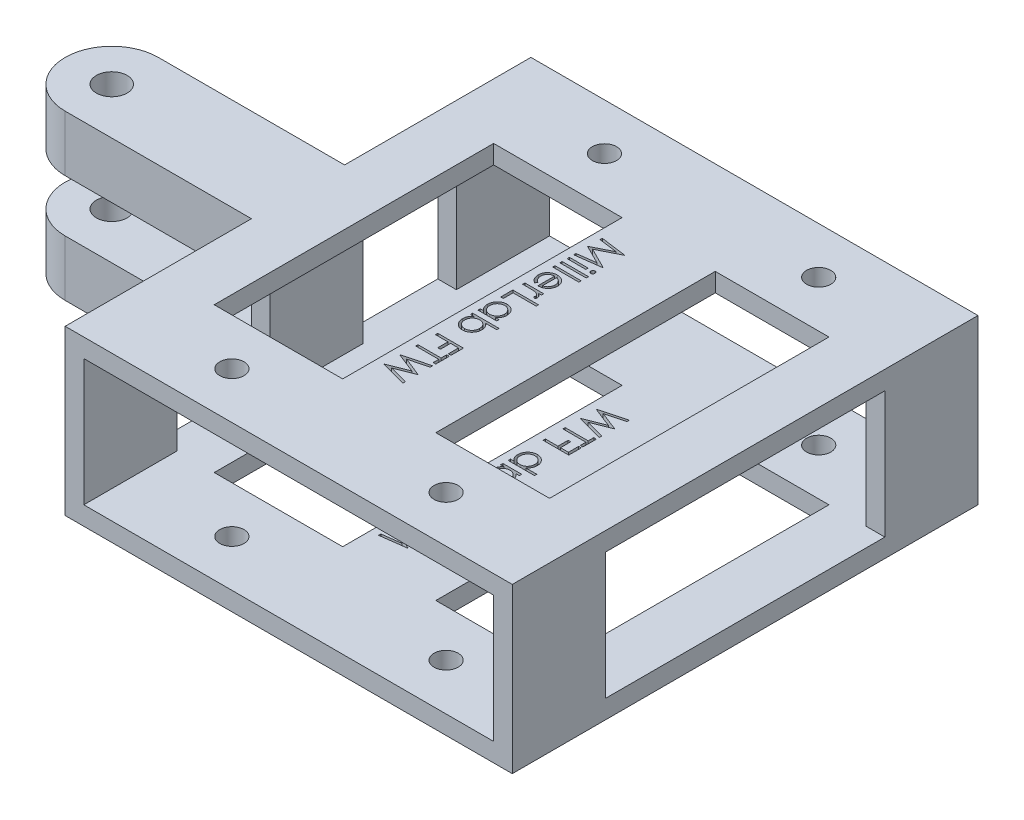
SolidWorks part; units mm, degrees
ref_plane "Front Plane" through (0, 0, 0) normal (0, 0, 1) x (1, 0, 0)
ref_plane "Top Plane" through (0, 0, 0) normal (0, 1, 0) x (1, 0, 0)
ref_plane "Right Plane" through (0, 0, 0) normal (1, 0, 0) x (0, 0, -1)
sketch "Sketch1" plane through (0, 0, 0) normal (0, 0, 1) x (1, 0, 0)
  line L0 (-30.48, -11.176) -> (30.48, -11.176)
  line L1 (-27.94, -8.636) -> (27.94, -8.636)
  line L2 (-27.94, -8.636) -> (-27.94, 8.636)
  line L3 (-27.94, 8.636) -> (27.94, 8.636)
  line L4 (27.94, -8.636) -> (27.94, 8.636)
  line L5 (-27.94, -8.636) -> (27.94, 8.636) construction
  line L6 (-27.94, 8.636) -> (27.94, -8.636) construction
  line L7 (30.48, -11.176) -> (30.48, 11.176)
  line L8 (-30.48, 11.176) -> (30.48, 11.176)
  line L9 (-30.48, -11.176) -> (-30.48, 11.176)
  point P0 (0, 0)
  dimension "D1" = 55.88
  dimension "D2" = 17.272
  dimension "D3" = 2.54
extrude "Boss-Extrude1" add sketch "Sketch1" against normal blind 12.7
sketch "Sketch2" plane through (0, 0, -12.7) normal (0, 0, -1) x (-1, 0, 0)
  line L0 (-27.94, 8.636) -> (27.94, 8.636) construction
  line L1 (-30.48, 11.176) -> (-22.86, 11.176)
  line L2 (-30.48, 11.176) -> (-30.48, 8.636)
  line L3 (-30.48, 8.636) -> (-22.86, 8.636)
  line L4 (-22.86, 11.176) -> (-22.86, 8.636)
  line L5 (-7.3566, 8.636) -> (-7.3566, 11.176)
  line L6 (-7.3566, 8.636) -> (5.3434, 8.636)
  line L7 (-7.3566, 11.176) -> (5.3434, 11.176)
  line L8 (5.3434, 8.636) -> (5.3434, 11.176)
  line L9 (-7.3566, 8.636) -> (5.3434, 11.176) construction
  line L10 (-7.3566, 11.176) -> (5.3434, 8.636) construction
  line L11 (-30.48, 0) -> (46.0926, 0) construction
  line L12 (30.48, 11.176) -> (22.86, 11.176)
  line L13 (30.48, 11.176) -> (30.48, 8.636)
  line L14 (30.48, 8.636) -> (22.86, 8.636)
  line L15 (22.86, 11.176) -> (22.86, 8.636)
  line L17 (-7.3566, -11.176) -> (5.3434, -8.636) construction
  line L18 (-7.3566, -8.636) -> (5.3434, -11.176) construction
  line L19 (22.86, -11.176) -> (22.86, -8.636)
  line L20 (30.48, -8.636) -> (22.86, -8.636)
  line L21 (30.48, -11.176) -> (30.48, -8.636)
  line L22 (30.48, -11.176) -> (22.86, -11.176)
  line L23 (5.3434, -8.636) -> (5.3434, -11.176)
  line L24 (-7.3566, -11.176) -> (5.3434, -11.176)
  line L25 (-7.3566, -8.636) -> (5.3434, -8.636)
  line L26 (-7.3566, -8.636) -> (-7.3566, -11.176)
  line L27 (-22.86, -11.176) -> (-22.86, -8.636)
  line L28 (-30.48, -8.636) -> (-22.86, -8.636)
  line L29 (-30.48, -11.176) -> (-30.48, -8.636)
  line L30 (-30.48, -11.176) -> (-22.86, -11.176)
  point P8 (-1.0066, 9.906)
  point P32 (-1.0066, -9.906)
  dimension "D1" = 7.62
  dimension "D2" = 12.7
extrude "Boss-Extrude2" add sketch "Sketch2" along normal blind 38.1
sketch "Sketch4" plane through (0, 0, -50.8) normal (0, 0, -1) x (-1, 0, 0)
  line L1 (-30.48, 11.176) -> (30.48, 11.176)
  line L2 (-30.48, 11.176) -> (-30.48, -11.176)
  line L3 (-30.48, -11.176) -> (30.48, -11.176)
  line L4 (30.48, 11.176) -> (30.48, -11.176)
  line L5 (-27.94, 8.636) -> (27.94, 8.636)
  line L6 (-27.94, 8.636) -> (-27.94, -8.636)
  line L7 (-27.94, -8.636) -> (27.94, -8.636)
  line L8 (27.94, 8.636) -> (27.94, -8.636)
extrude "Boss-Extrude3" add sketch "Sketch4" along normal blind 12.7
sketch "Sketch5" plane through (0, 11.176, 0) normal (0, 1, 0) x (1, 0, 0)
  line L0 (22.86, 12.7) -> (30.48, 12.7) construction
  line L1 (30.48, 63.5) -> (30.48, 0) construction
  line L2 (30.48, 12.7) -> (30.48, 0) construction
  line L3 (-30.48, 31.75) -> (30.48, 31.75) construction
  line L5 (-30.48, 63.5) -> (-30.48, 0) construction
  circle A0 centre (-14.1017, 6.35) radius 1.9939
  circle A1 centre (15.1083, 6.35) radius 1.9939
  circle A2 centre (15.1083, 57.15) radius 1.9939
  circle A3 centre (-14.1017, 57.15) radius 1.9939
  point P21 (-14.1017, 6.35)
  point P22 (15.1083, 6.35)
  dimension "D1" = 3.9878
  dimension "D2" = 3.9878
sketch "Sketch6" plane through (-30.48, 0, 0) normal (-1, 0, 0) x (0, 0, 1)
  line L0 (-63.5, 11.176) -> (0, 11.176) construction
  line L1 (-38.1, 11.176) -> (-25.4, 11.176)
  line L2 (-38.1, 11.176) -> (-38.1, -11.176)
  line L3 (-38.1, -11.176) -> (-25.4, -11.176)
  line L4 (-25.4, 11.176) -> (-25.4, -11.176)
  line L5 (-63.5, -11.176) -> (0, -11.176) construction
  line L7 (-50.8, -8.636) -> (-50.8, 8.636) construction
  dimension "D1" = 12.7
  dimension "D2" = 12.7
extrude "Boss-Extrude4" add sketch "Sketch6" against normal blind 2.54
sketch "Sketch7" plane through (-30.48, 0, 0) normal (-1, 0, 0) x (0, 0, 1)
  line L0 (-25.4, -8.636) -> (-25.4, 8.636) construction
  line L3 (-38.1, 8.636) -> (-25.4, 8.636)
  line L4 (-38.1, 8.636) -> (-38.1, 3.556)
  line L5 (-38.1, 3.556) -> (-25.4, 3.556)
  line L6 (-25.4, 8.636) -> (-25.4, 3.556)
  line L8 (-38.1, -8.636) -> (-25.4, -8.636)
  line L9 (-38.1, -8.636) -> (-38.1, -3.556)
  line L10 (-38.1, -3.556) -> (-25.4, -3.556)
  line L11 (-25.4, -8.636) -> (-25.4, -3.556)
  dimension "D1" = 5.08
extrude "Boss-Extrude5" add sketch "Sketch7" along normal blind 25.4
sketch "Sketch8" plane through (-55.88, 0, 0) normal (-1, 0, 0) x (0, 0, 1)
  line L0 (-31.75, 8.636) -> (-31.75, -8.636) construction
  line L1 (-25.4, 8.636) -> (-38.1, 8.636) construction
  line L2 (-38.1, -8.636) -> (-25.4, -8.636) construction
  line L4 (-31.75, 8.636) -> (-25.4, 8.636)
  line L5 (-31.75, 8.636) -> (-31.75, 3.556)
  line L6 (-31.75, 3.556) -> (-25.4, 3.556)
  line L7 (-25.4, 8.636) -> (-25.4, 3.556)
  line L8 (-25.4, -8.636) -> (-31.75, -8.636)
  line L9 (-25.4, -8.636) -> (-25.4, -3.556)
  line L10 (-25.4, -3.556) -> (-31.75, -3.556)
  line L11 (-31.75, -8.636) -> (-31.75, -3.556)
  dimension "D1" = 5.08
revolve "Revolve2" add sketch "Sketch8" angle 180 about L0
sketch "Sketch10" plane through (0, 8.636, 0) normal (0, 1, 0) x (1, 0, 0)
  line L0 (-55.88, 38.1) -> (-55.88, 25.4) construction
  line L1 (-62.23, 31.75) -> (-55.88, 31.75) construction
  arc A0 (-55.88, 38.1) -> (-55.88, 25.4) centre (-55.88, 31.75) ccw construction
  circle A1 centre (-55.88, 31.75) radius 2.0955
  dimension "D1" = 4.191
extrude "Cut-Extrude4" cut sketch "Sketch10" against normal through all
sketch "Sketch11" plane through (0, -11.176, 0) normal (0, -1, 0) x (-1, 0, 0)
  line L0 (4.2476, 12.7) -> (4.2476, 50.8) construction
  text T0 "MillerLab FTW"
extrude "Cut-Extrude7" cut sketch "Sketch11" against normal blind 2.54
sketch "Sketch14" plane through (0, 11.176, 0) normal (0, 1, 0) x (1, 0, 0)
  line L0 (-5.3434, 50.8) -> (-4.2476, 50.8) construction
  line L1 (-4.2476, 50.8) -> (-4.2476, 12.7) construction
  line L2 (-4.2476, 12.7) -> (-5.3434, 12.7) construction
  text T0 "MillerLab FTW"
extrude "Cut-Extrude8" cut sketch "Sketch14" against normal blind 2.54
hole_wizard "M4x0.7 Tapped Hole1" positions "Sketch16" profile "Sketch15" tap size "M4x0.7" standard "ANSI Metric" end condition through all
sketch "Sketch16" plane through (0, 11.176, 0) normal (0, 1, 0) x (1, 0, 0)
  point P0 (-14.1017, 57.15)
  point P3 (15.1083, 57.15)
  point P6 (15.1083, 6.35)
  point P9 (-14.1017, 6.35)
sketch "Sketch15" plane through (-14.1017, 11.176, -57.15) normal (1, 0, 0) x (0, 0, 1)
  line L0 (0, 0) -> (0, 22.352)
  line L1 (0, 22.352) -> (1.65, 22.352)
  line L2 (1.65, 22.352) -> (1.65, 0)
  line L5 (1.65, 0) -> (0, 0)
  line L11 (0, -6.35) -> (0, 107.95) construction
  dimension "Thru Tap Drill Dia." = 3.3
  dimension "Thru Tap Drill Depth" = 22.352
cosmetic thread "Hole Thread1" parameters "D2"=4
cosmetic thread "Hole Thread2" parameters "D2"=4
cosmetic thread "Hole Thread3" parameters "D2"=4
cosmetic thread "Hole Thread4" parameters "D2"=4
sketch "Sketch17" plane through (0, 8.636, 0) normal (0, 1, 0) x (1, 0, 0)
  line L0 (-55.88, 25.4) -> (-30.48, 25.4) construction
  line L1 (-55.88, 38.1) -> (-30.48, 38.1) construction
  line L2 (-30.48, 25.4) -> (-30.48, 38.1) construction
  line L3 (-55.88, 25.4) -> (-30.48, 25.4)
  line L4 (-55.88, 38.1) -> (-30.48, 38.1)
  line L5 (-30.48, 25.4) -> (-30.48, 38.1)
  arc A0 (-55.88, 38.1) -> (-55.88, 25.4) centre (-55.88, 31.75) ccw construction
  circle A1 centre (-55.88, 31.75) radius 2.0955 construction
  arc A2 (-55.88, 38.1) -> (-55.88, 25.4) centre (-55.88, 31.75) ccw
  circle A3 centre (-55.88, 31.75) radius 2.0955
extrude "Boss-Extrude6" add sketch "Sketch17" along normal blind 2.54
sketch "Sketch18" plane through (0, -8.636, 0) normal (0, -1, 0) x (1, 0, 0)
  line L0 (-30.48, -38.1) -> (-30.48, -25.4) construction
  line L1 (-55.88, -38.1) -> (-30.48, -38.1) construction
  line L2 (-55.88, -25.4) -> (-30.48, -25.4) construction
  line L3 (-30.48, -38.1) -> (-30.48, -25.4)
  line L4 (-55.88, -38.1) -> (-30.48, -38.1)
  line L5 (-55.88, -25.4) -> (-30.48, -25.4)
  arc A0 (-55.88, -25.4) -> (-55.88, -38.1) centre (-55.88, -31.75) ccw construction
  circle A1 centre (-55.88, -31.75) radius 2.0955 construction
  arc A2 (-55.88, -25.4) -> (-55.88, -38.1) centre (-55.88, -31.75) ccw
  circle A3 centre (-55.88, -31.75) radius 2.0955
extrude "Boss-Extrude7" add sketch "Sketch18" along normal blind 2.54
sketch "Sketch19" plane through (-30.48, 0, 0) normal (-1, 0, 0) x (0, 0, 1)
  line L0 (-63.5, 0) -> (0, 0) construction
  line L1 (-63.5, -11.176) -> (-63.5, 11.176) construction
